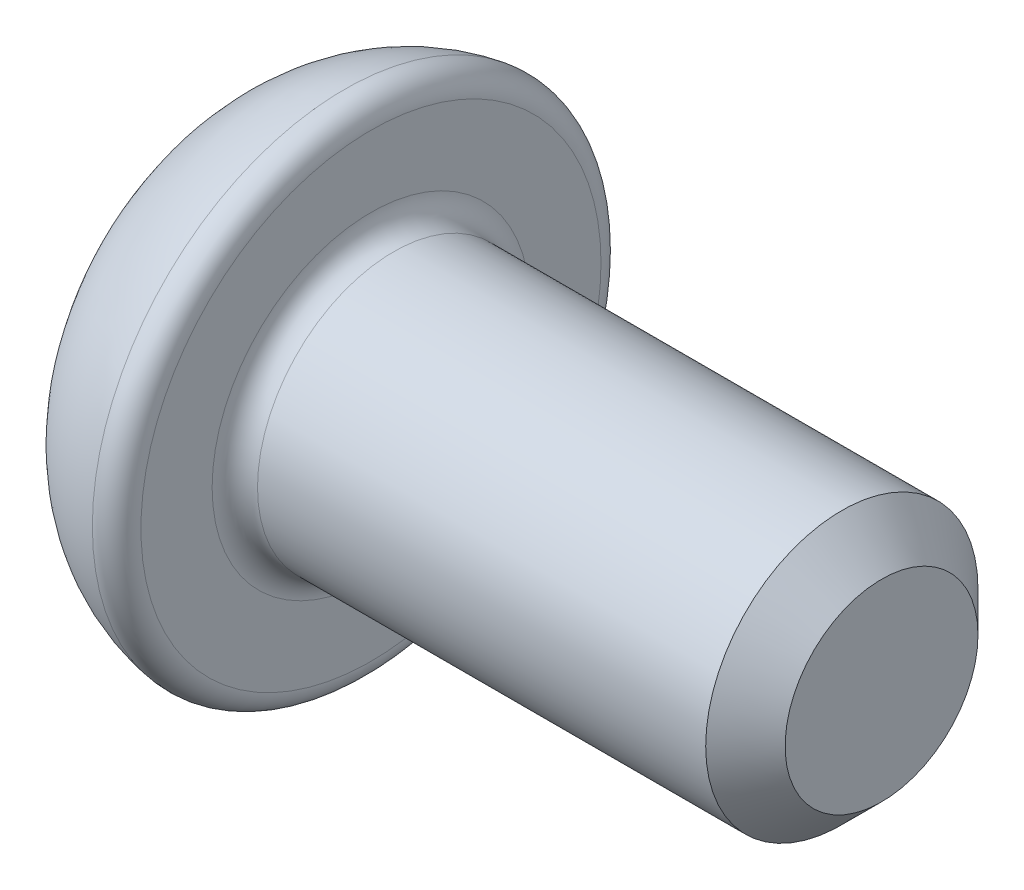
SolidWorks part; units mm, degrees
ref_plane "Front" through (0, 0, 0) normal (0, 0, 1) x (1, 0, 0)
ref_plane "Top" through (0, 0, 0) normal (0, 1, 0) x (1, 0, 0)
ref_plane "Right" through (0, 0, 0) normal (1, 0, 0) x (0, 0, -1)
sketch "Sketch1" plane through (0, 0, 0) normal (0, 0, 1) x (1, 0, 0)
  line L0 (0, 0) -> (0, 0.7429)
  line L1 (1.5, 2.0274) -> (1.5, 1.4)
  line L2 (1.7, 1.2) -> (5.65, 1.2)
  line L3 (5.65, 1.2) -> (6, 0.85)
  line L4 (6, 0.85) -> (6, 0)
  line L5 (6, 0) -> (0, 0)
  line L6 (0, 0) -> (-0.6746, 0) construction
  arc A0 (0, 0.7429) -> (1.2692, 2.225) centre (1.5, 0.7429) cw
  arc A1 (1.2692, 2.225) -> (1.5, 2.0274) centre (1.3, 2.0274) cw
  arc A2 (1.5, 1.4) -> (1.7, 1.2) centre (1.7, 1.4) ccw
  point P12 (0, 0)
  point P17 (1.2875, 2.027)
  point P18 (1.3424, 2.225)
  dimension "D1" = 2.4
  dimension "D5" = 0.2
  dimension "D6" = 1.5
  dimension "D2" = 135
  dimension "D3" = 0.35
  dimension "D4" = 1.5
  dimension "D7" = 4.45
  dimension "D8" = 4.5
revolve "Revolve1" add sketch "Sketch1" angle 360 about L6
sketch "Sketch2" plane through (0, 0, 0) normal (-1, 0, 0) x (0, 0, 1)
  line L1 (0.75, -0.433) -> (0.75, 0.433)
  line L2 (0.75, 0.433) -> (0, 0.866)
  line L3 (0, 0.866) -> (-0.75, 0.433)
  line L4 (-0.75, 0.433) -> (-0.75, -0.433)
  line L5 (-0.75, -0.433) -> (0, -0.866)
  line L6 (0, -0.866) -> (0.75, -0.433)
  circle A0 centre (0, 0) radius 0.75 construction
  point P1 (0, 0)
  dimension "D1" = 1.5
extrude "Cut-Extrude1" cut sketch "Sketch2" against normal blind 0.9
